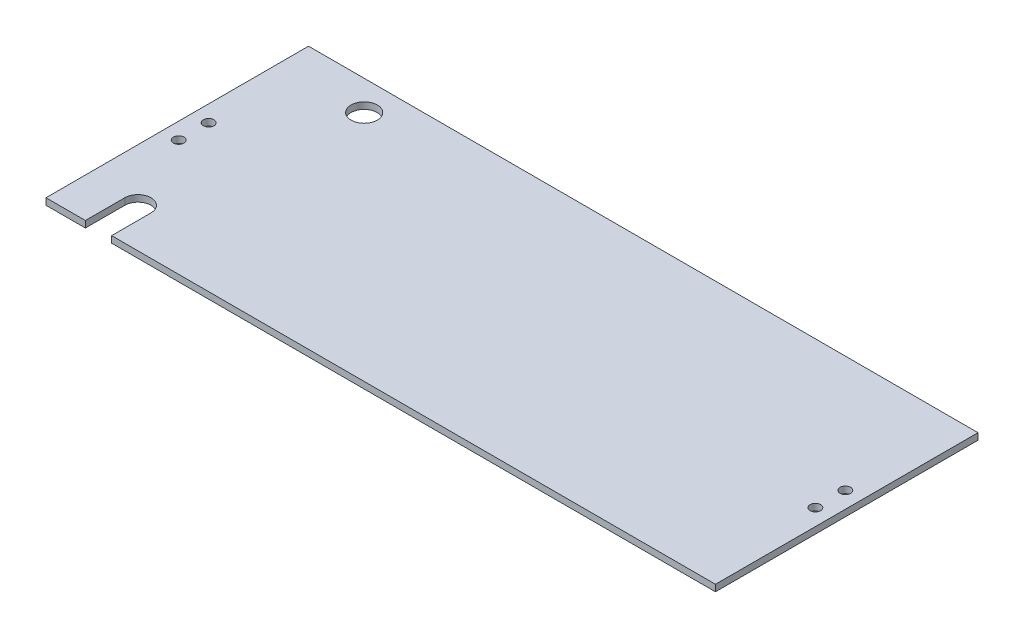
SolidWorks part; units mm, degrees
material "6061-T6 (SS)"
ref_plane "Front Plane" through (0, 0, 0) normal (0, 0, 1) x (1, 0, 0)
ref_plane "Top Plane" through (0, 0, 0) normal (0, 1, 0) x (1, 0, 0)
ref_plane "Right Plane" through (0, 0, 0) normal (1, 0, 0) x (0, 0, -1)
sketch "Sketch1" plane through (0, 0, 0) normal (0, 1, 0) x (1, 0, 0)
  line L1 (0, 0) -> (323.85, 0)
  line L2 (0, 0) -> (0, 127)
  line L3 (0, 127) -> (323.85, 127)
  line L4 (323.85, 0) -> (323.85, 127)
  dimension "D1" = 127
  dimension "D2" = 323.85
extrude "Boss-Extrude1" add sketch "Sketch1" along normal blind 3.175
sketch "Sketch2" plane through (0, 0, 0) normal (0, -1, 0) x (-1, 0, 0)
  line L3 (-19.05, 19.05) -> (-31.75, 19.05)
  line L4 (-25.4, 23.114) -> (-25.4, 0) construction
  line L5 (-33.274, 23.114) -> (-17.526, 23.114) construction
  line L6 (-19.05, 19.05) -> (-19.05, 0)
  line L7 (-19.05, 0) -> (-31.75, 0)
  line L9 (0, 0) -> (-323.85, 0) construction
  line L11 (-31.75, 19.05) -> (-31.75, 0)
  circle A0 centre (-41.275, 112.649) radius 6.35
  circle A1 centre (-25.4, 19.05) radius 6.35
  dimension "D6" = 12.7
extrude "Cut-Extrude1" cut sketch "Sketch2" against normal through all
hole_wizard "#10 Clearance Hole1" positions "Sketch4" profile "Sketch3" hole size "#10" standard "ANSI Inch"
sketch "Sketch4" plane through (0, 0, 0) normal (0, -1, 0) x (-1, 0, 0)
  point P0 (-315.9125, 70.75)
  point P3 (-315.9125, 56.25)
  point P6 (-7.9375, 70.75)
  point P9 (-7.9375, 56.25)
sketch "Sketch3" plane through (315.9125, 0, -70.75) normal (1, 0, 0) x (0, 0, -1)
  line L0 (0, 0) -> (0, 14.2338)
  line L1 (0, 14.2338) -> (2.5527, 12.7)
  line L2 (2.5527, 12.7) -> (2.5527, 0)
  line L5 (2.5527, 0) -> (0, 0)
  line L10 (0, 14.2338) -> (-2.5527, 12.7) construction
  line L11 (0, -6.35) -> (0, 107.95) construction
  dimension "Hole Dia." = 5.1054
  dimension "Hole Depth" = 12.7
  dimension "Drill Angle" = 118
